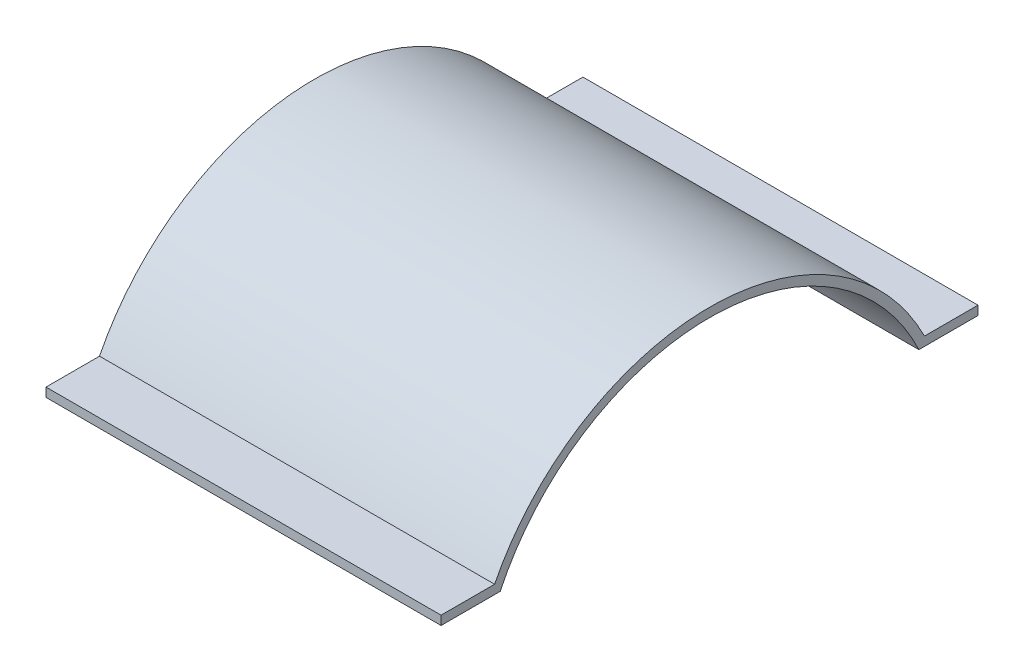
SolidWorks part; units mm, degrees
material "6061 Alloy"
ref_plane "Front Plane" through (0, 0, 0) normal (0, 0, 1) x (1, 0, 0)
ref_plane "Top Plane" through (0, 0, 0) normal (0, 1, 0) x (1, 0, 0)
ref_plane "Right Plane" through (0, 0, 0) normal (1, 0, 0) x (0, 0, -1)
sketch "Sketch1" plane through (0, 0, 0) normal (1, 0, 0) x (0, 0, -1)
  line L0 (18.0127, 0) -> (29.1207, 0)
  line L1 (-19.5712, 0) -> (-30.6793, 0)
  line L2 (-22.5793, -11.05) -> (21.0207, -11.05)
  line L3 (-30.6793, 0) -> (-30.6793, -11.05)
  line L4 (-30.6793, -11.05) -> (-22.5793, -11.05)
  line L5 (21.0207, -11.05) -> (29.1207, -11.05)
  line L6 (29.1207, -11.05) -> (29.1207, 0)
  line L7 (-30.6793, 0) -> (-30.6793, 1)
  line L8 (-30.6793, 1) -> (-24.7175, 1)
  line L9 (23.1589, 1) -> (29.1207, 1)
  line L166 (29.1207, 1) -> (29.1207, 0)
  arc A0 (21.0207, -11.05) -> (-22.5793, -11.05) centre (-0.7793, -11.05) ccw
  arc A3 (23.1589, 1) -> (-24.7175, 1) centre (-0.7793, -11.05) ccw
  arc A4 (22.5346, 0) -> (-24.0932, 0) centre (-0.7793, -11.05) ccw
  point P47 (34.4187, -11.05)
  dimension "D1" = 21.8
  dimension "D5" = 4
  dimension "D7" = 1
  dimension "D2" = 11.05
  dimension "D3" = 8.1
  dimension "D4" = 8.1
  dimension "D6" = 1
  dimension "D8" = 1
extrude "Boss-Extrude1" add sketch "Sketch1" along normal blind 44 contours A4 L0 L166 L9 A3 L8 L7 L1
